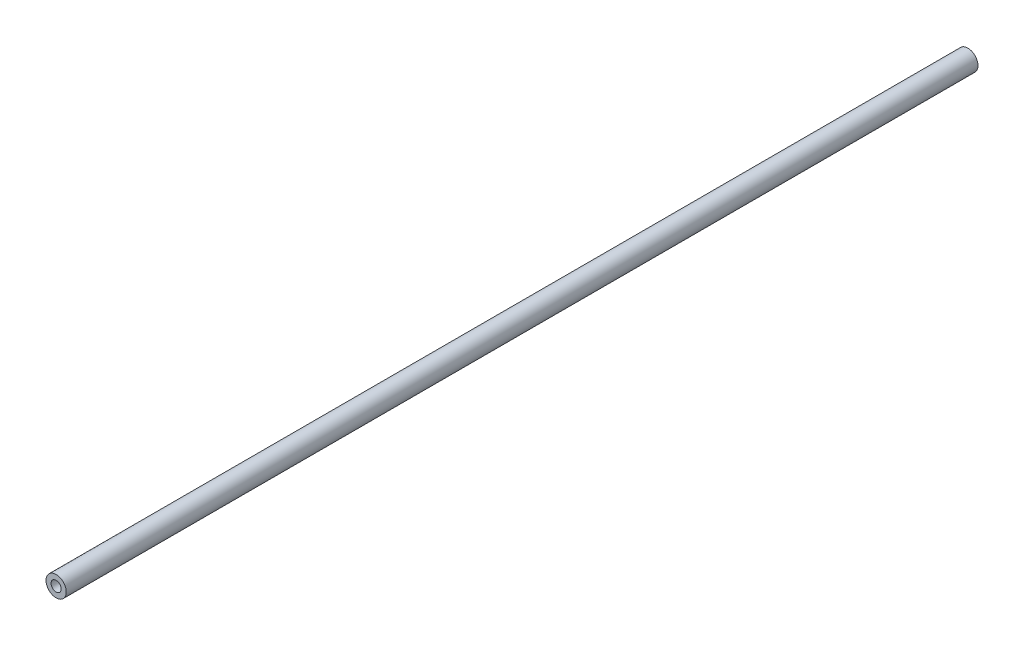
SolidWorks part; units mm, degrees
ref_plane "前视基准面" through (0, 0, 0) normal (0, 0, 1) x (1, 0, 0)
ref_plane "上视基准面" through (0, 0, 0) normal (0, 1, 0) x (1, 0, 0)
ref_plane "右视基准面" through (0, 0, 0) normal (1, 0, 0) x (0, 0, -1)
sketch "草图1" plane through (0, 0, 0) normal (0, 0, 1) x (1, 0, 0)
  circle A0 centre (0, 0) radius 1
  circle A1 centre (0, 0) radius 2
  dimension "D1" = 2
  dimension "D2" = 4
extrude "凸台-拉伸1" add sketch "草图1" along normal blind 180
sketch "草图2" plane through (0, 0, 180) normal (0, 0, 1) x (1, 0, 0)
  circle A1 centre (0, 0) radius 2
  circle A2 centre (0, 0) radius 2
  dimension "D1" = 0
